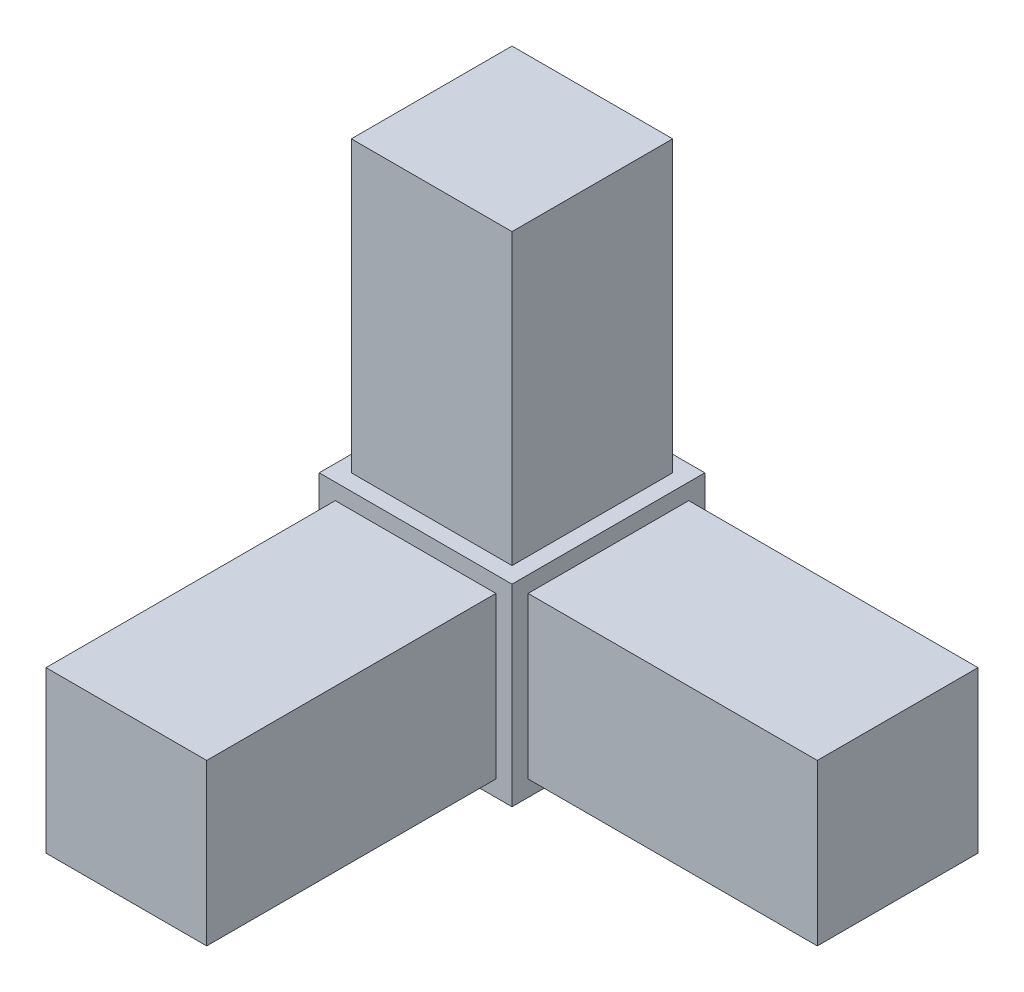
SolidWorks part; units mm, degrees
material "ABS"
ref_plane "Front Plane" through (0, 0, 0) normal (0, 0, 1) x (1, 0, 0)
ref_plane "Top Plane" through (0, 0, 0) normal (0, 1, 0) x (1, 0, 0)
ref_plane "Right Plane" through (0, 0, 0) normal (1, 0, 0) x (0, 0, -1)
sketch "Sketch1" plane through (0, 0, 0) normal (0, 0, 1) x (1, 0, 0)
  line L1 (9.525, -9.525) -> (-9.525, -9.525)
  line L2 (9.525, -9.525) -> (9.525, 9.525)
  line L3 (9.525, 9.525) -> (-9.525, 9.525)
  line L4 (-9.525, -9.525) -> (-9.525, 9.525)
  line L5 (9.525, -9.525) -> (-9.525, 9.525) construction
  line L6 (9.525, 9.525) -> (-9.525, -9.525) construction
  point P0 (0, 0)
  dimension "D1" = 19.05
extrude "Boss-Extrude1" add sketch "Sketch1" along normal blind 19.05
sketch "Sketch2" plane through (0, 9.525, 0) normal (0, 1, 0) x (1, 0, 0)
  line L0 (-9.525, 0) -> (9.525, -19.05) construction
  line L2 (-7.9375, -1.5875) -> (7.9375, -1.5875)
  line L3 (-7.9375, -1.5875) -> (-7.9375, -17.4625)
  line L4 (-7.9375, -17.4625) -> (7.9375, -17.4625)
  line L5 (7.9375, -1.5875) -> (7.9375, -17.4625)
  line L6 (-7.9375, -1.5875) -> (7.9375, -17.4625) construction
  line L7 (-7.9375, -17.4625) -> (7.9375, -1.5875) construction
  point P4 (0, -9.525)
  dimension "D1" = 15.875
extrude "Boss-Extrude2" add sketch "Sketch2" along normal blind 28.575
sketch "Sketch3" plane through (9.525, 0, 0) normal (1, 0, 0) x (0, 0, -1)
  line L0 (-19.05, 9.525) -> (0, -9.525) construction
  line L2 (-17.4625, -7.9375) -> (-1.5875, -7.9375)
  line L3 (-17.4625, -7.9375) -> (-17.4625, 7.9375)
  line L4 (-17.4625, 7.9375) -> (-1.5875, 7.9375)
  line L5 (-1.5875, -7.9375) -> (-1.5875, 7.9375)
  line L6 (-17.4625, -7.9375) -> (-1.5875, 7.9375) construction
  line L7 (-17.4625, 7.9375) -> (-1.5875, -7.9375) construction
  point P4 (-9.525, 0)
  dimension "D1" = 15.875
extrude "Boss-Extrude3" add sketch "Sketch3" along normal blind 28.575
sketch "Sketch4" plane through (0, 0, 19.05) normal (0, 0, 1) x (1, 0, 0)
  line L0 (-9.525, 9.525) -> (9.525, -9.525) construction
  line L2 (7.9375, -7.9375) -> (-7.9375, -7.9375)
  line L3 (7.9375, -7.9375) -> (7.9375, 7.9375)
  line L4 (7.9375, 7.9375) -> (-7.9375, 7.9375)
  line L5 (-7.9375, -7.9375) -> (-7.9375, 7.9375)
  line L6 (7.9375, -7.9375) -> (-7.9375, 7.9375) construction
  line L7 (7.9375, 7.9375) -> (-7.9375, -7.9375) construction
  point P4 (0, 0)
  dimension "D1" = 15.875
extrude "Boss-Extrude4" add sketch "Sketch4" along normal blind 28.575
equation "\"Height\"= 32in"
equation "\"Width\"= 23in"
equation "\"Depth\"= 20in"
equation "\"Plexi\"= .121in"
equation "\"MagnetThickness\"= .125in"
equation "\"MagnetDiameter\"= 12mm"
equation "\"DoorPlexi\" = \"Plexi\""
equation "\"BasePlateThickness\" = 0.5in"
equation "\"BasePlateWidth\" = \"Width\"+\"EBWidth\"-2*\"Plexi\""
equation "\"BasePlateDepth\" = \"TopBarDepth\"+2*\"CornerCube\""
equation "\"Boxsize\" = .75in"
equation "\"Boxinner\" = .625in"
equation "\"CornerCube\" = 0.75in"
equation "\"FingerLength\" = 1.125in"
equation "\"Cutwidth\"= .016in"
equation "\"Earsize\"= 1in + \"Cutwidth\" /2"
equation "\"Slotsize\" = 1in - \"CutWidth\" / 2"
equation "\"InnerWidth\" = \"Width\" - 2* \"Plexi\""
equation "\"InnerHeight\" = \"Height\" -2 * \"Plexi\""
equation "\"InnerDepth\" = \"Depth\" - 2*\"Plexi\""
equation "\"RearNumHoles\" = 4"
equation "\"RearHolesBorder\" = 2.25"
equation "\"RearHoleSpacing\" = (\"Width\" - 2*\"RearHolesBorder\") / (\"RearNumHoles\"-1)"
equation "\"RearBarLength\" = (\"InnerWidth\"-2*\"CornerCube\")"
equation "\"RearTopNumHoles\" = 4"
equation "\"RearTopHolesBorder\" = 3.1"
equation "\"RearTopHolesSpacing\" = (\"Width\" - 2*\"RearTopHolesBorder\") / (\"RearTopNumHoles\"-1)"
equation "\"SideTopNumHoles\" = 4"
equation "\"SideTopHoleOffset\"=\"CornerCube\"+\"FingerLength\"+\"Plexi\"+.5"
equation "\"SideTopHoleSpacing\" = (\"TopBarDepth\"-2*\"SideTopHoleOffset\") / (\"SideTopNumHoles\"-1)"
equation "\"SideHorizNumHoles\" = 4"
equation "\"SideHorizHoleBorder\" = 1.50"
equation "\"SideHorizHoleSpacing\" = (\"TopBarDepth\"-2*\"SideHorizHoleBorder\") / (\"SideHorizNumHoles\"-1)"
equation "\"SideVertBarLength\"=\"Height\"-\"BasePlateThickness\"-2*\"CornerCube\"-\"Plexi\""
equation "\"SideVertNumHoles\" = 4"
equation "\"SideVertHolesBorder\" = \"CornerCube\"+\"FingerLength\"+1.50"
equation "\"SideVertHoleSpacing\" = (\"InnerHeight\" - 2*\"SideVertHolesBorder\") / (\"SideVertNumHoles\"-1)"
equation "\"RearSideVertNumHoles\" = 4"
equation "\"RearSideVertHolesBorder\" = 2.4"
equation "\"RearSideVertHoleSpacing\" = (\"InnerHeight\" - 2*\"RearSideVertHolesBorder\") / (\"RearSideVertNumHoles\"-1)"
equation "\"RivetDia\" = .228in"
equation "\"SlotDepth\" = \"Plexi\" + 0.75in + .005in"
equation "\"SideSlotWidth\"   = \"Plexi\"+.005in"
equation "\"SidePanelVertSpacing\" = (\"Height\"-2*(1.75-\"Plexi\")) / 5"
equation "\"BottomPanelSideHoleSpacing\" = (\"InnerDepth\"-2*(1.75-\"Plexi\")) / 4"
equation "\"FrontDoorGap\" = .1in"
equation "\"TopDepth\" = \"Depth\"-\"DoorPlexi\"-\"FrontDoorGap\""
equation "\"TopBarDepth\" = \"Depth\"-\"DoorPlexi\"-\"Plexi\"-2*\"MagnetThickness\"-2*\"CornerCube\""
equation "\"D1@Boss-Extrude1\"=\"CornerCube\""
equation "\"D1@Sketch1\"=\"CornerCube\""
equation "\"D1@Boss-Extrude4\"=\"FingerLength\""
equation "\"D1@Boss-Extrude3\"=\"FingerLength\""
equation "\"D1@Boss-Extrude2\"=\"FingerLength\""
equation "\"D1@Sketch2\"=\"Boxinner\""
equation "\"D1@Sketch3\"=\"Boxinner\""
equation "\"D1@Sketch4\"=\"Boxinner\""
